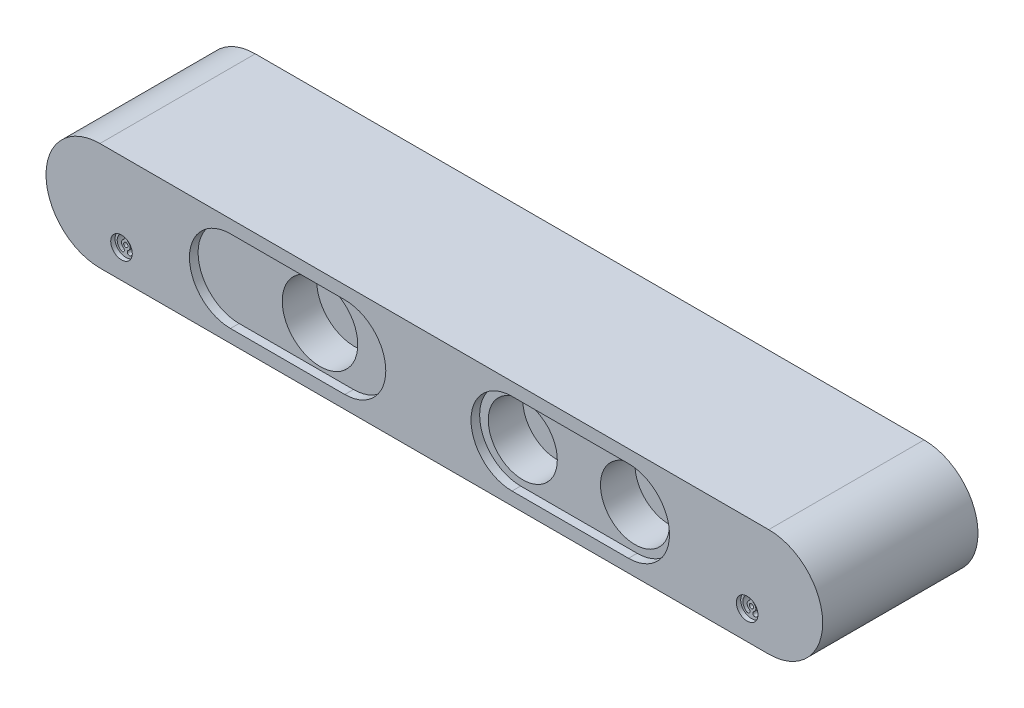
SolidWorks part; units mm, degrees
ref_plane "Front Plane" through (0, 0, 0) normal (0, 0, 1) x (1, 0, 0)
ref_plane "Top Plane" through (0, 0, 0) normal (0, 1, 0) x (1, 0, 0)
ref_plane "Right Plane" through (0, 0, 0) normal (1, 0, 0) x (0, 0, -1)
sketch "Sketch1" plane through (0, 0, 0) normal (0, 0, 1) x (1, 0, 0)
  line L0 (-77.5, 0) -> (77.5, 0) construction
  line L1 (-77.5, 12.5) -> (77.5, 12.5)
  line L2 (-77.5, -12.5) -> (77.5, -12.5)
  arc A0 (-77.5, 12.5) -> (-77.5, -12.5) centre (-77.5, 0) ccw
  arc A1 (77.5, -12.5) -> (77.5, 12.5) centre (77.5, 0) ccw
  point P3 (0, 0)
  dimension "D1" = 12.5
  dimension "D3" = 0
  dimension "D2" = 155
extrude "Boss-Extrude1" add sketch "Sketch1" against normal blind 36
sketch "Sketch3" plane through (0, 0, 0) normal (0, 0, 1) x (1, 0, 0)
  circle A0 centre (-28.5, 0) radius 8.75
  circle A1 centre (18.5, 0) radius 8
  circle A2 centre (44.5, 0) radius 8
  dimension "D1" = 17.5
  dimension "D4" = 16
  dimension "D7" = 16
  dimension "D2" = 28.5
  dimension "D3" = 0
  dimension "D5" = 47
  dimension "D6" = 73
  dimension "D8" = 0
  dimension "D9" = 0
extrude "Cut-Extrude1" cut sketch "Sketch3" against normal blind 10
sketch "Sketch4" plane through (0, 0, 0) normal (0, 0, 1) x (1, 0, 0)
  line L0 (-47.25, 0) -> (-20.75, 0) construction
  line L1 (-47.25, 9.5) -> (-20.75, 9.5)
  line L2 (-47.25, -9.5) -> (-20.75, -9.5)
  line L3 (18, 0) -> (45, 0) construction
  line L4 (18, 9.5) -> (45, 9.5)
  line L5 (18, -9.5) -> (45, -9.5)
  arc A0 (-47.25, 9.5) -> (-47.25, -9.5) centre (-47.25, 0) ccw
  arc A1 (-20.75, -9.5) -> (-20.75, 9.5) centre (-20.75, 0) ccw
  arc A2 (18, 9.5) -> (18, -9.5) centre (18, 0) ccw
  arc A3 (45, -9.5) -> (45, 9.5) centre (45, 0) ccw
  point P3 (-34, 0)
  point P8 (31.5, 0)
  dimension "D1" = 9.5
  dimension "D2" = 9.5
  dimension "D6" = 31.5
  dimension "D3" = 26.5
  dimension "D4" = 34
  dimension "D5" = 27
extrude "Cut-Extrude2" cut sketch "Sketch4" against normal blind 2
sketch "Sketch5" plane through (0, 0, 0) normal (0, 0, 1) x (1, 0, 0)
  circle A0 centre (72.5, -5.8596) radius 2.5
  circle A1 centre (-72.5, -5.8596) radius 2.5
  dimension "D1" = 5
  dimension "D2" = 5
  dimension "D3" = 72.5
  dimension "D4" = 72.5
extrude "Cut-Extrude3" cut sketch "Sketch5" against normal blind 1
sketch "Sketch6" plane through (0, 0, 0) normal (0, 0, 1) x (1, 0, 0)
  circle A0 centre (-72.5, -5.8596) radius 0.5
  circle A1 centre (72.5, -5.8596) radius 0.5
  arc A2 (-71.6708, -4.6096) -> (-71.6708, -7.1096) centre (-72.5, -5.8596) cw construction
  arc A3 (-71.3945, -7.5262) -> (-71.3945, -4.1929) centre (-72.5, -5.8596) ccw
  arc A4 (-71.9472, -6.6929) -> (-71.9472, -5.0262) centre (-72.5, -5.8596) ccw
  arc A5 (-71.9472, -6.6929) -> (-71.3945, -7.5262) centre (-71.6708, -7.1096) ccw
  arc A6 (-71.3945, -4.1929) -> (-71.9472, -5.0262) centre (-71.6708, -4.6096) ccw
  arc A7 (-73.3292, -4.6096) -> (-73.3292, -7.1096) centre (-72.5, -5.8596) ccw construction
  arc A8 (-73.6055, -4.1929) -> (-73.6055, -7.5262) centre (-72.5, -5.8596) ccw
  arc A9 (-73.0528, -5.0262) -> (-73.0528, -6.6929) centre (-72.5, -5.8596) ccw
  arc A10 (-73.0528, -5.0262) -> (-73.6055, -4.1929) centre (-73.3292, -4.6096) ccw
  arc A11 (-73.6055, -7.5262) -> (-73.0528, -6.6929) centre (-73.3292, -7.1096) ccw
  arc A12 (73.3292, -4.6096) -> (73.3292, -7.1096) centre (72.5, -5.8596) cw construction
  arc A13 (73.6055, -7.5262) -> (73.6055, -4.1929) centre (72.5, -5.8596) ccw
  arc A14 (73.0528, -6.6929) -> (73.0528, -5.0262) centre (72.5, -5.8596) ccw
  arc A15 (73.0528, -6.6929) -> (73.6055, -7.5262) centre (73.3292, -7.1096) ccw
  arc A16 (73.6055, -4.1929) -> (73.0528, -5.0262) centre (73.3292, -4.6096) ccw
  arc A17 (71.6708, -4.6096) -> (71.6708, -7.1096) centre (72.5, -5.8596) ccw construction
  arc A18 (71.3945, -4.1929) -> (71.3945, -7.5262) centre (72.5, -5.8596) ccw
  arc A19 (71.9472, -5.0262) -> (71.9472, -6.6929) centre (72.5, -5.8596) ccw
  arc A20 (71.9472, -5.0262) -> (71.3945, -4.1929) centre (71.6708, -4.6096) ccw
  arc A21 (71.3945, -7.5262) -> (71.9472, -6.6929) centre (71.6708, -7.1096) ccw
  circle A22 centre (72.5, -5.8596) radius 2.5 construction
  point P8 (-71, -5.8596)
  point P16 (-74, -5.8596)
  point P23 (74, -5.8596)
  point P31 (71, -5.8596)
  dimension "D2" = 1
  dimension "D5" = 0.5
  dimension "D6" = 2.5
  dimension "D9" = 0.5
  dimension "D11" = 1
  dimension "D14" = 0.5
  dimension "D18" = 0.5
  dimension "D3" = 0
  dimension "D4" = 1.5
  dimension "D7" = 0
  dimension "D8" = 2.5
  dimension "D10" = 1.5
  dimension "D12" = 0
  dimension "D13" = 1.5
  dimension "D15" = 2.5
  dimension "D16" = 0
  dimension "D17" = 2.5
  dimension "D19" = 1.5
  dimension "D21" = 0
extrude "Cut-Extrude4" cut sketch "Sketch6" against normal blind 5
sketch "Sketch7" plane through (0, -12.5, 0) normal (0, -1, 0) x (1, 0, 0)
  line L0 (-77.5, 0) -> (77.5, 0) construction
  line L1 (3, -10.5) -> (6.8, -10.5)
  line L2 (3, -10.5) -> (3, -25.5)
  line L3 (3, -25.5) -> (6.8, -25.5)
  line L4 (6.8, -10.5) -> (6.8, -25.5)
  line L6 (-3, -10.5) -> (-6.8, -10.5)
  line L7 (-3, -10.5) -> (-3, -25.5)
  line L8 (-3, -25.5) -> (-6.8, -25.5)
  line L9 (-6.8, -10.5) -> (-6.8, -25.5)
  dimension "D1" = 3.8
  dimension "D2" = 15
  dimension "D3" = 10.5
  dimension "D4" = 3
  dimension "D5" = 3.8
  dimension "D6" = 15
  dimension "D7" = 3
  dimension "D8" = 10.5
